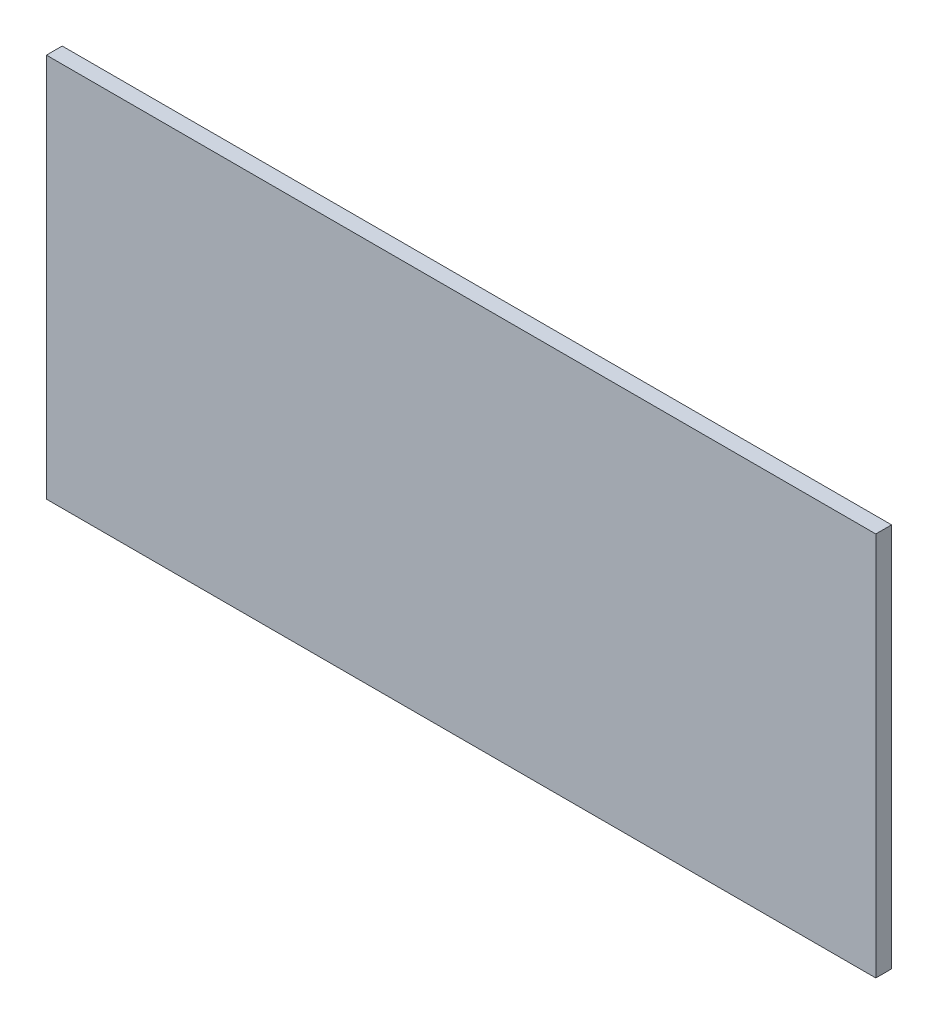
SolidWorks part; units mm, degrees
ref_plane "Ebene vorne" through (0, 0, 0) normal (0, 0, 1) x (1, 0, 0)
ref_plane "Ebene oben" through (0, 0, 0) normal (0, 1, 0) x (1, 0, 0)
ref_plane "Ebene rechts" through (0, 0, 0) normal (1, 0, 0) x (0, 0, -1)
sketch "Sketch1" plane through (0, 0, 0) normal (0, 0, 1) x (1, 0, 0)
  line L1 (-578, -268) -> (578, -268)
  line L2 (-578, -268) -> (-578, 268)
  line L3 (-578, 268) -> (578, 268)
  line L4 (578, -268) -> (578, 268)
  line L5 (-578, -268) -> (578, 268) construction
  line L6 (-578, 268) -> (578, -268) construction
  point P0 (0, 0)
  dimension "D1" = 1156
  dimension "D2" = 536
extrude "Boss-Extrude1" add sketch "Sketch1" along normal blind 22
